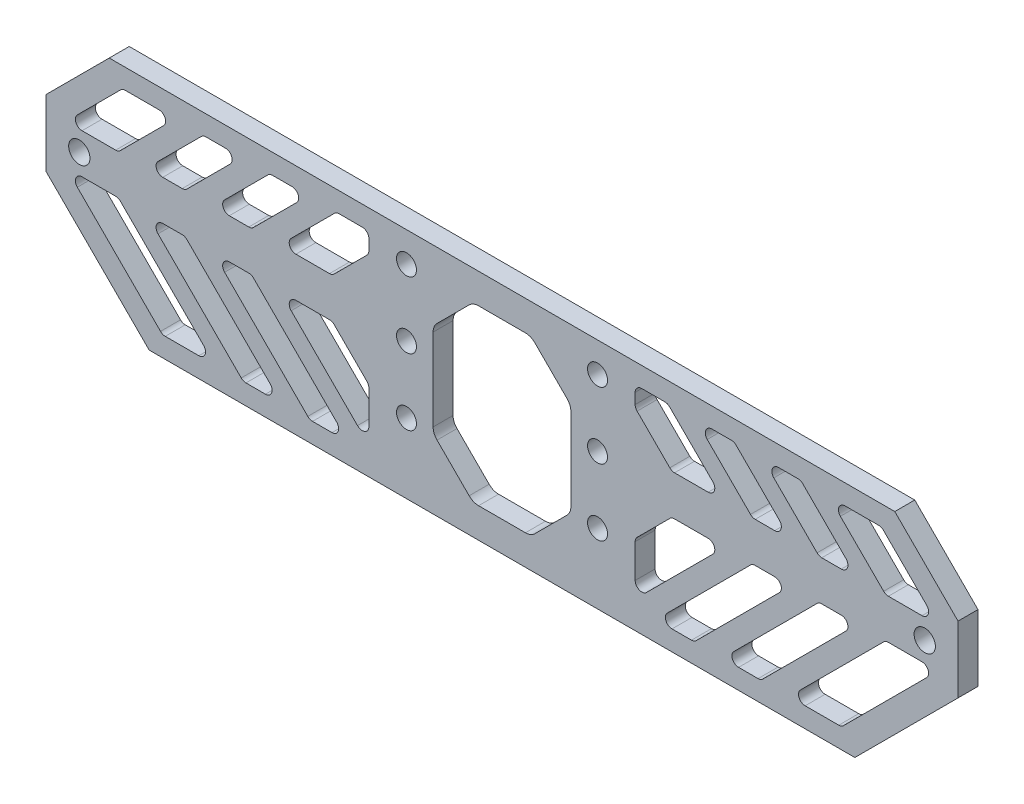
SolidWorks part; units mm, degrees
material "Thornel Mat VMA"
ref_plane "前视基准面" through (0, 0, 0) normal (0, 0, 1) x (1, 0, 0)
ref_plane "上视基准面" through (0, 0, 0) normal (0, 1, 0) x (1, 0, 0)
ref_plane "右视基准面" through (0, 0, 0) normal (1, 0, 0) x (0, 0, -1)
sketch "草图1" plane through (0, 0, 0) normal (0, 0, 1) x (1, 0, 0)
  line L1 (-16.35, 14.5) -> (16.35, 14.5)
  line L2 (-16.35, 14.5) -> (-16.35, -14.5)
  line L3 (-16.35, -14.5) -> (16.35, -14.5)
  line L4 (16.35, 14.5) -> (16.35, -14.5)
  line L5 (-16.35, 14.5) -> (16.35, -14.5) construction
  line L6 (-16.35, -14.5) -> (16.35, 14.5) construction
  line L7 (-14.35, 10) -> (14.35, 10) construction
  line L8 (-14.35, 10) -> (-14.35, -10) construction
  line L9 (-14.35, -10) -> (14.35, -10) construction
  line L10 (14.35, 10) -> (14.35, -10) construction
  line L11 (-14.35, 10) -> (14.35, -10) construction
  line L12 (-14.35, -10) -> (14.35, 10) construction
  circle A0 centre (-14.35, -10) radius 1.5
  circle A1 centre (-14.35, 10) radius 1.5
  circle A2 centre (14.35, 10) radius 1.5
  circle A3 centre (14.35, -10) radius 1.5
  circle A4 centre (-14.35, 0) radius 1.5
  circle A5 centre (14.35, 0) radius 1.5
  point P0 (0, 0)
  point P6 (0, 0)
  dimension "D5" = 3
  dimension "D1" = 29
  dimension "D2" = 28.7
  dimension "D3" = 32.7
  dimension "D4" = 20
extrude "凸台-拉伸1" add sketch "草图1" along normal blind 3
chamfer "倒角1" distance 3 angle 45 4 edges at (16.35, -14.5, 1.5) (16.35, 14.5, 1.5) (-16.35, -14.5, 1.5) (-16.35, 14.5, 1.5)
sketch "草图2" plane through (0, 0, 3) normal (0, 0, 1) x (1, 0, 0)
  line L0 (-11, 7) -> (-8, 10)
  line L1 (-8, 10) -> (8, 10)
  line L2 (-11, 7) -> (-11, -7)
  line L3 (-8, -10) -> (8, -10)
  line L4 (11, 7) -> (11, -7)
  line L5 (-11, 10) -> (11, -10) construction
  line L6 (-11, -10) -> (11, 10) construction
  line L7 (8, 10) -> (11, 7)
  line L8 (-11, -7) -> (-8, -10)
  line L9 (8, -10) -> (11, -7)
  point P0 (0, 0)
  dimension "D1" = 22
  dimension "D2" = 20
extrude "切除-拉伸1" [suppressed] cut sketch "草图2" against normal through all
fillet "圆角1" [suppressed] radius 1
sketch "草图3" plane through (0, 0, 3) normal (0, 0, 1) x (1, 0, 0)
  line L1 (-68.5, 14.5) -> (68.5, 14.5)
  line L2 (-68.5, 14.5) -> (-68.5, -14.5)
  line L3 (-68.5, -14.5) -> (68.5, -14.5)
  line L4 (68.5, 14.5) -> (68.5, -14.5)
  line L5 (-68.5, 14.5) -> (68.5, -14.5) construction
  line L6 (-68.5, -14.5) -> (68.5, 14.5) construction
  line L8 (16.35, -11.5) -> (16.35, 11.5)
  line L9 (16.35, 11.5) -> (13.35, 14.5)
  line L10 (13.35, 14.5) -> (-13.35, 14.5)
  line L11 (-13.35, 14.5) -> (-16.35, 11.5)
  line L12 (-16.35, 11.5) -> (-16.35, -11.5)
  line L13 (-16.35, -11.5) -> (-13.35, -14.5)
  line L14 (-13.35, -14.5) -> (13.35, -14.5)
  line L15 (13.35, -14.5) -> (16.35, -11.5)
  line L16 (16.35, -11.5) -> (16.35, 11.5)
  line L17 (16.35, 11.5) -> (13.35, 14.5)
  line L18 (13.35, 14.5) -> (-13.35, 14.5)
  line L19 (-13.35, 14.5) -> (-16.35, 11.5)
  line L20 (-16.35, 11.5) -> (-16.35, -11.5)
  line L21 (-16.35, -11.5) -> (-13.35, -14.5)
  line L22 (-13.35, -14.5) -> (13.35, -14.5)
  line L23 (13.35, -14.5) -> (16.35, -11.5)
  point P2 (0, 0)
  dimension "D2" = 137
  dimension "D1" = 0
extrude "凸台-拉伸2" add sketch "草图3" against normal up to surface (3 mm away) up to face at (0, 0, 0)
chamfer "倒角2" distance 9.5 4 edges at (68.5, -14.5, 1.5) (68.5, 14.5, 1.5) (-68.5, 14.5, 1.5) (-68.5, -14.5, 1.5)
sketch "草图4" plane through (0, 0, 0) normal (0, 0, -1) x (-1, 0, 0)
  line L0 (-59, -14.5) -> (-53, -20.5)
  line L1 (-53, -20.5) -> (53, -20.5)
  line L2 (53, -20.5) -> (59, -14.5)
  line L3 (59, -14.5) -> (-59, -14.5)
  line L4 (-68.5, -5) -> (-59, -14.5) construction
  line L5 (59, -14.5) -> (68.5, -5) construction
  dimension "D3" = 6
extrude "凸台-拉伸3" add sketch "草图4" against normal up to surface (3 mm away) up to face at (0, 0, 3)
sketch "草图6" plane through (0, 0, 0) normal (0, 0, -1) x (-1, 0, 0)
  circle A0 centre (-63.5, 0) radius 1.6
  dimension "D2" = 3.2
  dimension "D1" = 63.5
extrude "切除-拉伸2" cut sketch "草图6" against normal through all
sketch "草图7" plane through (0, 0, 0) normal (0, 0, -1) x (-1, 0, 0)
  line L24 (-65.5, 3) -> (-57, 11.5)
  line L29 (-65.5, -3) -> (-51, -17.5)
  line L30 (-55.5, -3) -> (-41, -17.5)
  line L32 (-68.5, 0) -> (0, 0)
  line L33 (-68.5, -5) -> (-68.5, 5) construction
  line L34 (-68.5, -3) -> (0, -3)
  line L35 (-68.5, 3) -> (0, 3)
  line L36 (-20, 14.5) -> (-20, -20.5)
  line L37 (-59, 14.5) -> (59, 14.5) construction
  line L38 (-53, -20.5) -> (53, -20.5) construction
  line L39 (-20, -20.5) -> (-53, -20.5)
  line L40 (-53, -20.5) -> (-68.5, -5)
  line L41 (-68.5, -5) -> (-68.5, 5)
  line L42 (-68.5, 5) -> (-59, 14.5)
  line L43 (-59, 14.5) -> (-20, 14.5)
  line L44 (-59, 14.5) -> (-68.5, 5) construction
  line L45 (-57.7574, 11.5) -> (-23, 11.5)
  line L47 (-23, -17.5) -> (-51.7574, -17.5)
  line L48 (-51.7574, -17.5) -> (-65.5, -3.7574)
  line L49 (-65.5, -3.7574) -> (-65.5, 3.7574)
  line L50 (-65.5, 3.7574) -> (-57.7574, 11.5)
  line L51 (-23, 11.5) -> (-20, 11.5)
  line L52 (-23, -17.5) -> (-20, -17.5)
  line L53 (-55.5, 3) -> (-47, 11.5)
  line L54 (-45.5, -3) -> (-31, -17.5)
  line L55 (-45.5, 3) -> (-37, 11.5)
  line L56 (-35.5, -3) -> (-21, -17.5)
  line L57 (-35.5, 3) -> (-27, 11.5)
  line L58 (-25.5, -3) -> (-11, -17.5)
  line L59 (-25.5, 3) -> (-17, 11.5)
  line L60 (-57.6213, -3) -> (-42.0607, -18.5607)
  line L61 (-47.6213, -3) -> (-32.0607, -18.5607)
  line L62 (-37.6213, -3) -> (-22.0607, -18.5607)
  line L63 (-34.4393, 1.9393) -> (-24.8787, 11.5)
  line L64 (-44.4393, 1.9393) -> (-34.8787, 11.5)
  line L65 (-54.4393, 1.9393) -> (-44.8787, 11.5)
  line L66 (-54.4393, -1.9393) -> (-38.8787, -17.5)
  line L67 (-44.4393, -1.9393) -> (-28.8787, -17.5)
  line L68 (-34.4393, -1.9393) -> (-19.9393, -16.4393)
  line L69 (-37.6213, 3) -> (-28.0607, 12.5607)
  line L70 (-47.6213, 3) -> (-38.0607, 12.5607)
  line L71 (-57.6213, 3) -> (-48.0607, 12.5607)
  line L72 (-56.5607, 4.0607) -> (-48.0607, 12.5607) construction
  line L73 (-54.4393, 1.9393) -> (-45.9393, 10.4393) construction
  line L74 (-36.5607, 4.0607) -> (-28.0607, 12.5607) construction
  line L75 (-44.4393, 1.9393) -> (-35.9393, 10.4393) construction
  line L76 (-34.4393, 1.9393) -> (-25.9393, 10.4393) construction
  line L77 (-54.4393, -1.9393) -> (-39.9393, -16.4393) construction
  line L78 (-46.5607, -4.0607) -> (-32.0607, -18.5607) construction
  line L79 (-44.4393, -1.9393) -> (-29.9393, -16.4393) construction
  line L80 (-36.5607, -4.0607) -> (-22.0607, -18.5607) construction
  line L81 (-46.5607, 4.0607) -> (-38.0607, 12.5607) construction
  line L82 (-56.5607, -4.0607) -> (-42.0607, -18.5607) construction
  line L113 (-23, 11.5) -> (-23, -17.5) construction
  dimension "D1" = 3
  dimension "D2" = 3
  dimension "D3" = 20
  dimension "D4" = 3
  dimension "D5" = 1.5
  dimension "D6" = 1.5
  dimension "D7" = 5
  dimension "D8" = 5.5
extrude "切除-拉伸4" cut sketch "草图7" against normal blind 10 contours L35 L71 L45 L24 | L60 L34 L29 L47 | L34 L66 L47 L61 | L35 L70 L45 L65 | L35 L69 L45 L64 | L34 L67 L47 L62 | L34 L68 L36 L58 | L63 L35 L59 L36 L51 L45
fillet "圆角2" radius 1 33 edges at (33.1213, -17.5, 1.5) (38.8787, -17.5, 1.5) (53.3787, -3, 1.5) (47.6213, -3, 1.5) (51, -17.5, 1.5) (65.5, -3, 1.5) (57.6213, -3, 1.5) (43.1213, -17.5, 1.5) (20, -8.5, 1.5) (20, -16.3787, 1.5) (33.3787, -3, 1.5) (25.5, -3, 1.5) (23.1213, -17.5, 1.5) (28.8787, -17.5, 1.5) (43.3787, -3, 1.5) (37.6213, -3, 1.5) (20, 11.5, 1.5) (20, 8.5, 1.5) (25.5, 3, 1.5) (33.3787, 3, 1.5) (24.8787, 11.5, 1.5) (57, 11.5, 1.5) (49.1213, 11.5, 1.5) (53.3787, 3, 1.5) (44.8787, 11.5, 1.5) (39.1213, 11.5, 1.5) (47.6213, 3, 1.5) (43.3787, 3, 1.5) (34.8787, 11.5, 1.5) (29.1213, 11.5, 1.5) (37.6213, 3, 1.5) (57.6213, 3, 1.5) (65.5, 3, 1.5)
mirror "镜向1" about plane through (0, 0, 0) normal (1, 0, 0) of "切除-拉伸2", "切除-拉伸4", "圆角2"
sketch "草图8" plane through (0, 0, 3) normal (0, 0, 1) x (1, 0, 0)
  line L0 (0, 14.5) -> (0, -20.5) construction
  line L1 (10.35, -16) -> (-10.35, -16)
  line L2 (10.35, -16) -> (10.35, 10)
  line L3 (10.35, 10) -> (-10.35, 10)
  line L4 (-10.35, -16) -> (-10.35, 10)
  line L5 (10.35, -16) -> (-10.35, 10) construction
  line L6 (10.35, 10) -> (-10.35, -16) construction
  line L7 (59, 14.5) -> (-59, 14.5) construction
  line L8 (53, -20.5) -> (-53, -20.5) construction
  line L11 (-14.35, 10) -> (-10.35, 10) construction
  point P0 (0, -3)
  dimension "D1" = 4
  dimension "D2" = 4.5
extrude "切除-拉伸5" cut sketch "草图8" against normal blind 10
chamfer "倒角3" distance 6 angle 45 4 edges at (-10.35, -16, 1.5) (10.35, -16, 1.5) (10.35, 10, 1.5) (-10.35, 10, 1.5)
fillet "圆角3" radius 2 8 edges at (10.35, -10, 1.5) (4.35, -16, 1.5) (-10.35, -10, 1.5) (-10.35, 4, 1.5) (-4.35, 10, 1.5) (4.35, 10, 1.5) (10.35, 4, 1.5) (-4.35, -16, 1.5)
